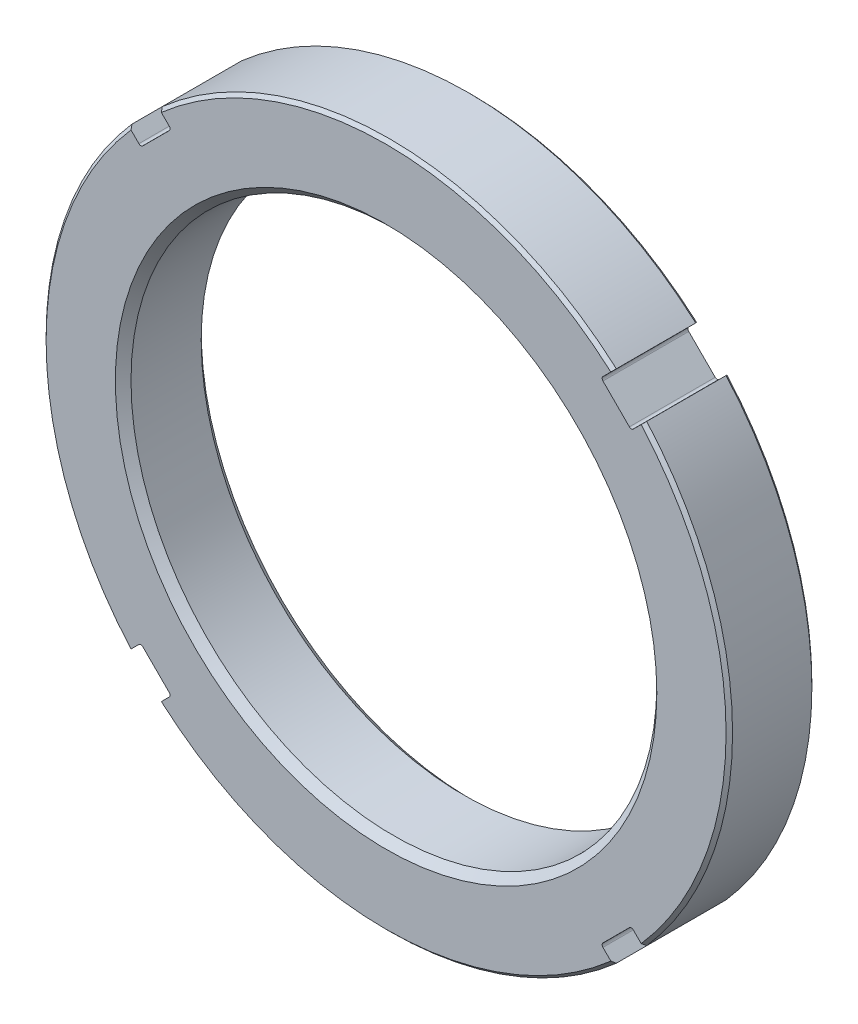
SolidWorks part; units mm, degrees
material "Alloy Steel"
ref_plane "Front Plane" through (0, 0, 0) normal (0, 0, 1) x (1, 0, 0)
ref_plane "Top Plane" through (0, 0, 0) normal (0, 1, 0) x (1, 0, 0)
ref_plane "Right Plane" through (0, 0, 0) normal (1, 0, 0) x (0, 0, -1)
sketch "Sketch1" plane through (0, 0, 0) normal (0, 0, 1) x (1, 0, 0)
  circle A0 centre (0, 0) radius 50.8
  circle A1 centre (0, 0) radius 38.9128
  dimension "D1" = 101.6
  dimension "D2" = 77.8256
extrude "Extrude1" add sketch "Sketch1" along normal blind 12.7
chamfer "Chamfer1" distance 0.4803 angle 45 2 edges at (50.8, 0, 0) (50.8, 0, 12.7)
chamfer "Chamfer2" distance 1.1557 angle 45 2 edges at (38.9128, 0, 0) (38.9128, 0, 12.7)
sketch "Sketch2" plane through (0, 0, 12.7) normal (0, 0, 1) x (1, 0, 0)
  line L0 (0, 0) -> (22.7176, 0) construction
  line L1 (0, 0) -> (15.6425, 15.6425) construction
  line L2 (33.6057, 38.0959) -> (31.8081, 36.2982)
  line L3 (31.8081, 36.2982) -> (36.2982, 31.8081)
  line L4 (38.0959, 33.6057) -> (36.2982, 31.8081)
  circle A0 centre (0, 0) radius 50.8 construction
  arc A1 (38.0959, 33.6057) -> (33.6057, 38.0959) centre (0, 0) ccw
  dimension "D3" = 2.6416
  dimension "D1" = 45
  dimension "D2" = 6.35
extrude "Cut-Extrude1" cut sketch "Sketch2" against normal through all
fillet "Fillet1" radius 0.4064 2 edges at (36.2982, 31.8081, 6.35) (31.8081, 36.2982, 6.35)
pattern_circular "CirPattern1" count 4 over 360 about axis through (0, 0, 0) along (0, 0, 1) of "Fillet1", "Cut-Extrude1"
